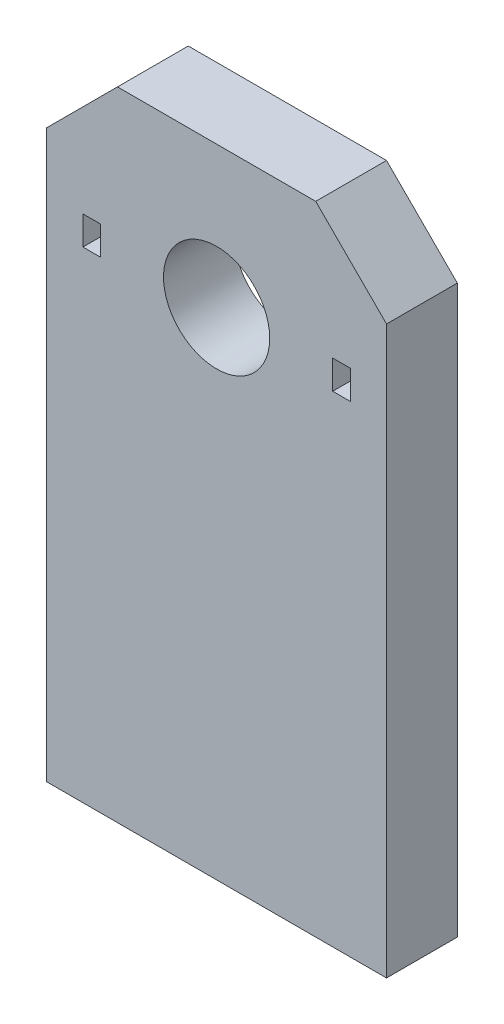
SolidWorks part; units mm, degrees
ref_plane "Front Plane" through (0, 0, 0) normal (0, 0, 1) x (1, 0, 0)
ref_plane "Top Plane" through (0, 0, 0) normal (0, 1, 0) x (1, 0, 0)
ref_plane "Right Plane" through (0, 0, 0) normal (1, 0, 0) x (0, 0, -1)
sketch "Sketch1" plane through (0, 0, 0) normal (0, 0, 1) x (1, 0, 0)
  line L0 (-15.24, 57.15) -> (-15.24, 0)
  line L1 (-15.24, 57.15) -> (15.24, 57.15)
  line L2 (-15.24, 0) -> (15.24, 0)
  line L3 (15.24, 57.15) -> (15.24, 0)
  line L4 (-15.24, 57.15) -> (15.24, 0) construction
  line L5 (-15.24, 0) -> (15.24, 57.15) construction
  line L6 (0, 44.45) -> (-15.24, 44.45) construction
  line L7 (0, 44.45) -> (15.24, 44.45) construction
  line L8 (0, -3.4925) -> (0, 3.4925) construction
  line L9 (-11.9888, 45.739) -> (-10.414, 45.739)
  line L10 (-11.9888, 45.739) -> (-11.9888, 43.1609)
  line L11 (-11.9888, 43.1609) -> (-10.414, 43.1609)
  line L12 (-10.414, 45.739) -> (-10.414, 43.1609)
  line L13 (-11.9888, 45.739) -> (-10.414, 43.1609) construction
  line L14 (-11.9888, 43.1609) -> (-10.414, 45.739) construction
  line L15 (10.414, 45.739) -> (11.9888, 45.739)
  line L16 (10.414, 45.739) -> (10.414, 43.1609)
  line L17 (10.414, 43.1609) -> (11.9888, 43.1609)
  line L18 (11.9888, 45.739) -> (11.9888, 43.1609)
  line L19 (10.414, 45.739) -> (11.9888, 43.1609) construction
  line L20 (10.414, 43.1609) -> (11.9888, 45.739) construction
  line L21 (3.4925, 0) -> (-3.4925, 0) construction
  circle A0 centre (0, 44.45) radius 4.7625
  point P1 (0, 28.575)
  point P9 (-11.2014, 44.45)
  point P14 (11.2014, 44.45)
  dimension "D8" = 9.525
  dimension "D1" = 2.5781
  dimension "D3" = 1.5748
  dimension "D4" = 1.5748
  dimension "D5" = 10.414
  dimension "D6" = 10.414
  dimension "D7" = 30.48
  dimension "D9" = 57.15
  dimension "D10" = 12.7
extrude "Boss-Extrude1" add sketch "Sketch1" along normal blind 6.35
chamfer "Chamfer1" distance 6.35 angle 45 2 edges at (15.24, 57.15, 3.175) (-15.24, 57.15, 3.175)
